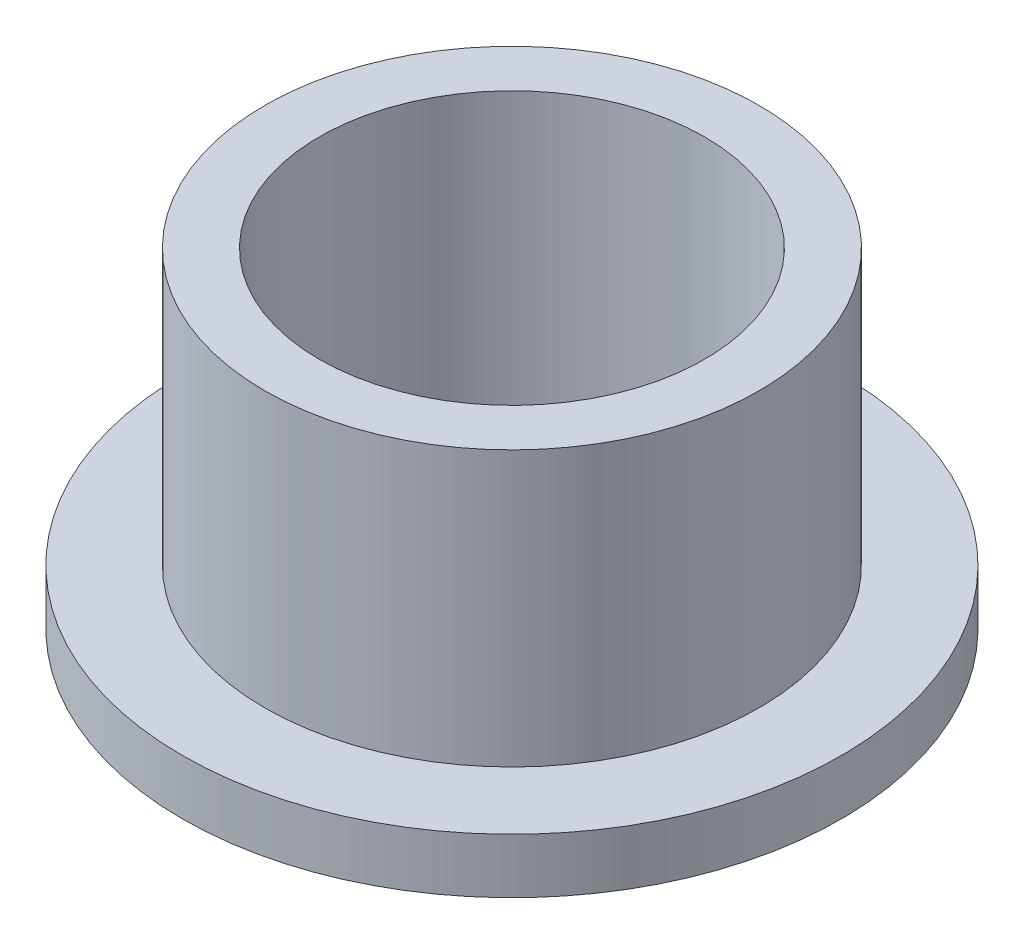
SolidWorks part; units mm, degrees
ref_plane "Front" through (0, 0, 0) normal (0, 0, 1) x (1, 0, 0)
ref_plane "Top" through (0, 0, 0) normal (0, 1, 0) x (1, 0, 0)
ref_plane "Right" through (0, 0, 0) normal (1, 0, 0) x (0, 0, -1)
sketch "Sketch1" plane through (0, 0, 0) normal (0, 1, 0) x (1, 0, 0)
  circle A0 centre (0, 0) radius 11.1379
  circle A1 centre (0, 0) radius 14.2875
  circle A2 centre (0, 0) radius 19.05
  dimension "ID" = 22.2758
  dimension "OD" = 28.575
  dimension "FlangeOD" = 38.1
sketch "Sketch2" plane through (0, 0, 0) normal (0, 1, 0) x (1, 0, 0)
  circle A0 centre (0, 0) radius 11.1379 construction
  circle A1 centre (0, 0) radius 14.2875 construction
  circle A2 centre (0, 0) radius 11.1379
  circle A3 centre (0, 0) radius 14.2875
extrude "Boss-Extrude1" add sketch "Sketch2" along normal blind 19.05
sketch "Sketch3" plane through (0, 0, 0) normal (0, 1, 0) x (1, 0, 0)
  circle A0 centre (0, 0) radius 19.05 construction
  circle A1 centre (0, 0) radius 14.2875 construction
  circle A2 centre (0, 0) radius 19.05
  circle A3 centre (0, 0) radius 14.2875
extrude "Boss-Extrude2" add sketch "Sketch3" along normal blind 3.175
